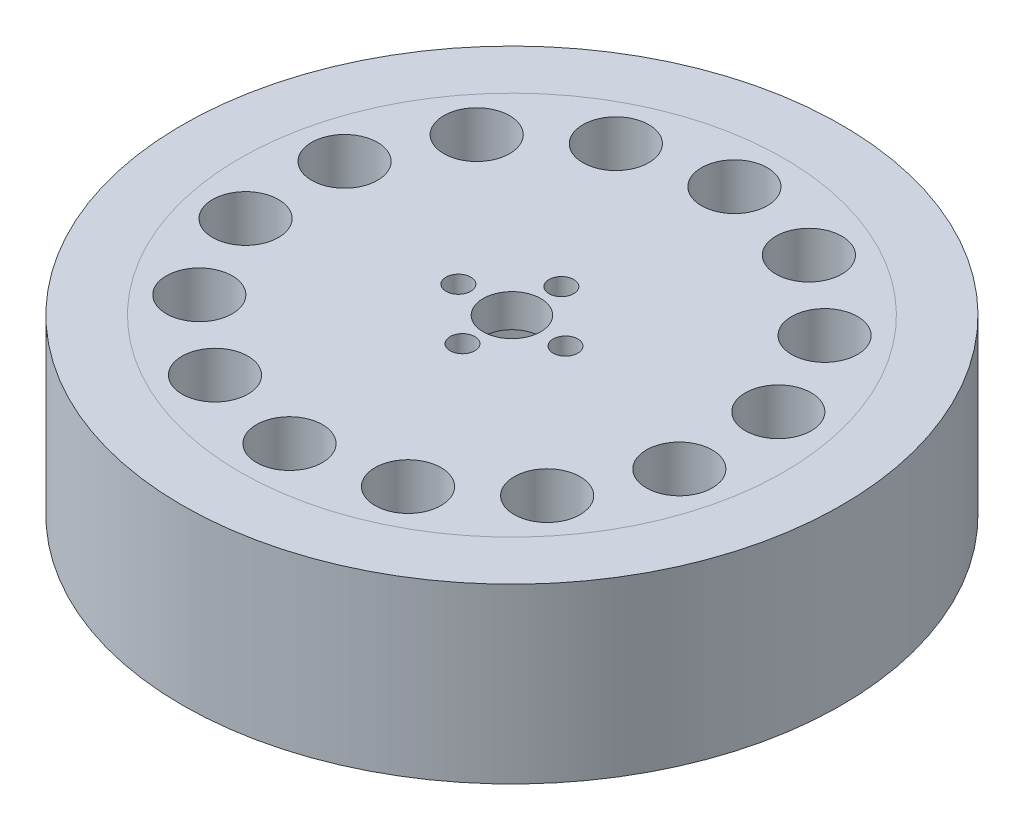
SolidWorks part; units mm, degrees
ref_plane "前视基准面" through (0, 0, 0) normal (0, 0, 1) x (1, 0, 0)
ref_plane "上视基准面" through (0, 0, 0) normal (0, 1, 0) x (1, 0, 0)
ref_plane "右视基准面" through (0, 0, 0) normal (1, 0, 0) x (0, 0, -1)
sketch "草图1" plane through (0, 0, 0) normal (0, 1, 0) x (1, 0, 0)
  circle A0 centre (0, 0) radius 21
  circle A1 centre (0, 0) radius 33
  circle A2 centre (0, 0) radius 27 construction
  circle A3 centre (0, 27) radius 4
  circle A4 centre (11.7149, 24.3262) radius 4
  circle A5 centre (21.1095, 16.8342) radius 4
  circle A6 centre (26.3231, 6.0081) radius 4
  circle A7 centre (26.3231, -6.0081) radius 4
  circle A8 centre (21.1095, -16.8342) radius 4
  circle A9 centre (11.7149, -24.3262) radius 4
  circle A10 centre (0, -27) radius 4
  circle A11 centre (-11.7149, -24.3262) radius 4
  circle A12 centre (-21.1095, -16.8342) radius 4
  circle A13 centre (-26.3231, -6.0081) radius 4
  circle A14 centre (-26.3231, 6.0081) radius 4
  circle A15 centre (-21.1095, 16.8342) radius 4
  circle A16 centre (-11.7149, 24.3262) radius 4
  point P7 (12.2893, 21.9097)
  point P8 (0, 0)
  point P36 (0, 0)
  dimension "D1" = 42
  dimension "D2" = 66
  dimension "D3" = 54
  dimension "D4" = 8
  dimension "D5" = 14
extrude "凸台-拉伸1" add sketch "草图1" along normal mid plane 21
sketch "草图2" plane through (0, 10.5, 0) normal (0, 1, 0) x (1, 0, 0)
  circle A0 centre (0, 0) radius 21 construction
  circle A1 centre (0, 0) radius 21
  circle A2 centre (0, 0) radius 6.5 construction
  circle A3 centre (0, 0) radius 6 construction
  circle A4 centre (0, 6) radius 1.5
  circle A5 centre (0, -6) radius 1.5
  circle A6 centre (-6.5, 0) radius 1.5
  circle A7 centre (6.5, 0) radius 1.5
  circle A8 centre (0, 0) radius 3.5
  point P15 (0.1199, 0)
  dimension "D1" = 12
  dimension "D2" = 13
  dimension "D3" = 3
  dimension "D4" = 7
extrude "凸台-拉伸2" add sketch "草图2" against normal offset from surface (4 mm away) 17 up to face at (0, -10.5, 33)
sketch "草图3" plane through (0, 10.5, 0) normal (0, 1, 0) x (1, 0, 0)
  circle A0 centre (0, 0) radius 40
  circle A1 centre (0, 0) radius 33 construction
  circle A2 centre (0, 0) radius 33
  dimension "D1" = 80
extrude "凸台-拉伸3" add sketch "草图3" against normal blind 21 separate body
